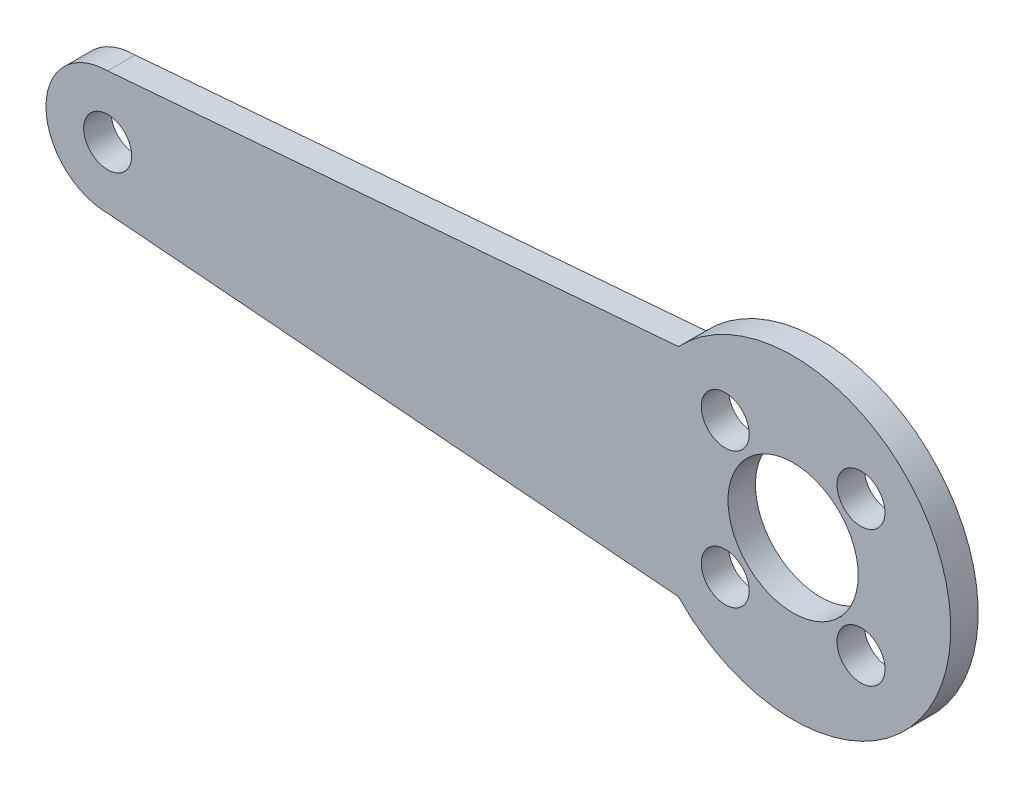
SolidWorks part; units mm, degrees
ref_plane "前视基准面" through (0, 0, 0) normal (0, 0, 1) x (1, 0, 0)
ref_plane "上视基准面" through (0, 0, 0) normal (0, 1, 0) x (1, 0, 0)
ref_plane "右视基准面" through (0, 0, 0) normal (1, 0, 0) x (0, 0, -1)
sketch "草图1" plane through (0, 0, 0) normal (0, 0, 1) x (1, 0, 0)
  line L0 (0, 0) -> (-50, 0) construction
  line L1 (-50, 4.5) -> (-8.3544, 7.9028)
  line L2 (-50, -4.5) -> (-8.3544, -7.9028)
  line L3 (4.9497, -4.9497) -> (4.9497, 4.9497) construction
  line L4 (4.9497, -4.9497) -> (-4.9497, -4.9497) construction
  line L5 (4.9497, -4.9497) -> (4.9497, 4.9497) construction
  line L6 (4.9497, 4.9497) -> (-4.9497, 4.9497) construction
  line L7 (-4.9497, -4.9497) -> (-4.9497, 4.9497) construction
  line L8 (4.9497, -4.9497) -> (-4.9497, 4.9497) construction
  line L9 (4.9497, 4.9497) -> (-4.9497, -4.9497) construction
  line L10 (-4.9497, -4.9497) -> (4.9497, -4.9497) construction
  line L11 (-4.9497, 4.9497) -> (-4.9497, -4.9497) construction
  arc A0 (-8.3544, -7.9028) -> (-8.3544, 7.9028) centre (0, 0) ccw
  arc A1 (-50, 4.5) -> (-50, -4.5) centre (-50, 0) ccw
  circle A2 centre (-50, 0) radius 1.75
  circle A3 centre (4.9497, 4.9497) radius 1.75
  circle A4 centre (4.9497, -4.9497) radius 1.75
  circle A5 centre (-4.9497, -4.9497) radius 1.75
  circle A6 centre (-4.9497, 4.9497) radius 1.75
  point P27 (0, 0)
  dimension "D1" = 23
  dimension "D2" = 9
  dimension "D4" = 3.5
  dimension "D7" = 3.5
  dimension "D3" = 50
  dimension "D5" = 90
  dimension "D6" = 14
  dimension "D8" = 4
extrude "凸台-拉伸1" add sketch "草图1" along normal blind 2 contours L1 A0 L2 A1 | A2 | A3 | A6 | A4 | A5
sketch "草图2" plane through (0, 0, 2) normal (0, 0, 1) x (1, 0, 0)
  circle A0 centre (0, 0) radius 4.75
  dimension "D1" = 9.5
extrude "切除-拉伸1" cut sketch "草图2" against normal blind 2
